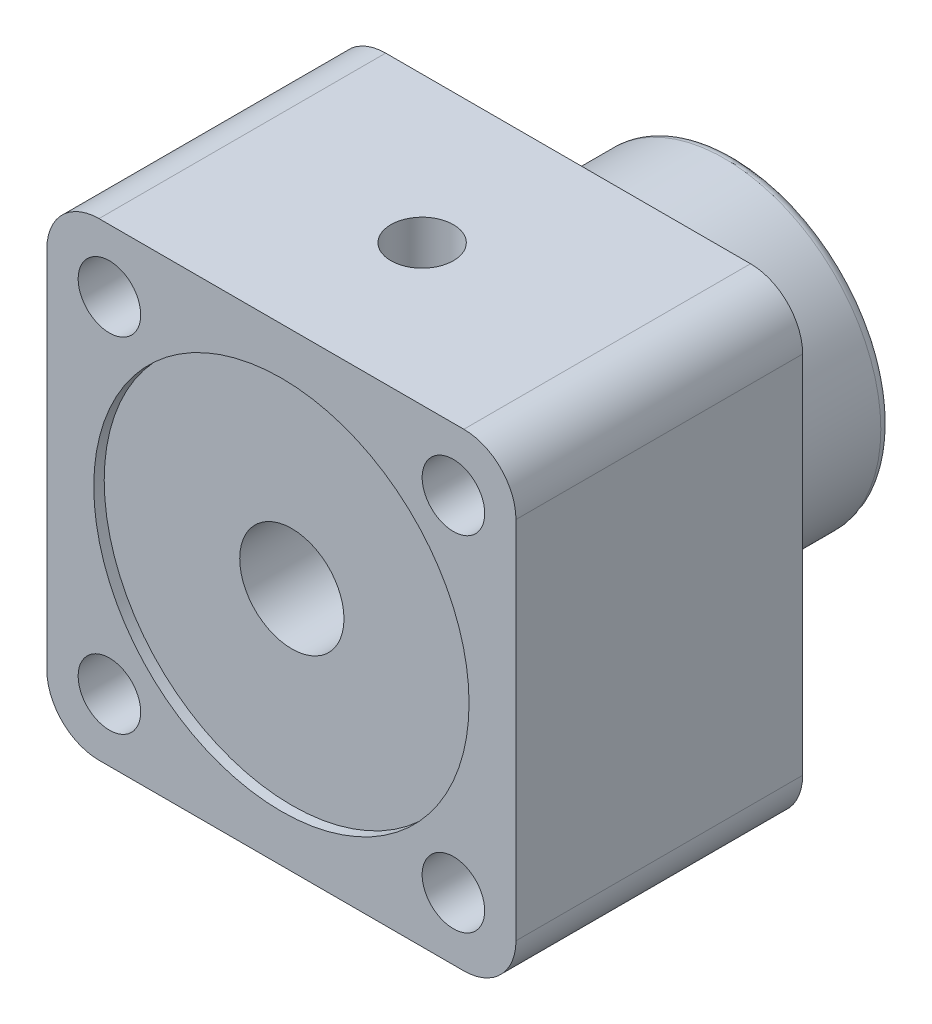
SolidWorks part; units mm, degrees
ref_plane "Front Plane" through (0, 0, 0) normal (0, 0, 1) x (1, 0, 0)
ref_plane "Top Plane" through (0, 0, 0) normal (0, 1, 0) x (1, 0, 0)
ref_plane "Right Plane" through (0, 0, 0) normal (1, 0, 0) x (0, 0, -1)
sketch "Sketch1" plane through (0, 0, 0) normal (0, 0, 1) x (1, 0, 0)
  line L0 (0, 40) -> (0, 5)
  line L1 (-5, 45) -> (-40, 45)
  line L2 (-45, 40) -> (-45, 5)
  line L3 (-40, 0) -> (-5, 0)
  line L6 (-45, 0) -> (0, 45) construction
  line L9 (-45, 45) -> (0, 0) construction
  circle A0 centre (-6, 39) radius 3
  circle A1 centre (-6, 6) radius 3
  circle A2 centre (-39, 6) radius 3
  circle A3 centre (-39, 39) radius 3
  arc A4 (-40, 45) -> (-45, 40) centre (-40, 40) ccw
  arc A5 (0, 40) -> (-5, 45) centre (-5, 40) ccw
  arc A6 (-45, 5) -> (-40, 0) centre (-40, 5) ccw
  arc A7 (-5, 0) -> (0, 5) centre (-5, 5) ccw
  dimension "D5" = 6
  dimension "D7" = 5
  dimension "D8" = 5
  dimension "D9" = 5
  dimension "D2" = 45
  dimension "D3" = 45
  dimension "D11" = 33
extrude "Boss-Extrude1" add sketch "Sketch1" along normal blind 27.5
sketch "Sketch3" plane through (0, 0, 27.5) normal (0, 0, 1) x (1, 0, 0)
  line L0 (-43.5355, 1.4645) -> (-1.4645, 43.5355) construction
  line L1 (-43.5355, 43.5355) -> (-1.4645, 1.4645) construction
  arc A0 (-45, 5) -> (-40, 0) centre (-40, 5) ccw construction
  arc A1 (0, 40) -> (-5, 45) centre (-5, 40) ccw construction
  arc A2 (-40, 45) -> (-45, 40) centre (-40, 40) ccw construction
  arc A3 (-5, 0) -> (0, 5) centre (-5, 5) ccw construction
  circle A4 centre (-22.5, 22.5) radius 18
  dimension "D1" = 36
extrude "Cut-Extrude1" cut sketch "Sketch3" against normal blind 1
sketch "Sketch4" plane through (0, 0, 0) normal (0, 0, -1) x (-1, 0, 0)
  line L0 (0, 5) -> (0, 40) construction
  line L1 (5, 45) -> (40, 45) construction
  circle A0 centre (22.5, 22.5) radius 5
  dimension "D1" = 10
  dimension "D2" = 22.5
  dimension "D3" = 22.5
extrude "Cut-Extrude2" cut sketch "Sketch4" against normal through all
sketch "Sketch5" plane through (0, 0, 0) normal (0, 0, -1) x (-1, 0, 0)
  circle A0 centre (22.5, 22.5) radius 15
  circle A1 centre (22.5, 22.5) radius 5 construction
  circle A2 centre (22.5, 22.5) radius 5
  dimension "D1" = 30
extrude "Boss-Extrude2" add sketch "Sketch5" along normal blind 16
fillet "Fillet1" radius 1 1 edges at (-37.5, 22.5, -16)
sketch "Sketch6" plane through (0, 45, 0) normal (0, 1, 0) x (1, 0, 0)
  line L0 (-45, -27.5) -> (-45, 0) construction
  line L2 (-5, 0) -> (-40, 0) construction
  circle A0 centre (-22.5, -14) radius 3
  dimension "D1" = 6
  dimension "D2" = 22.5
  dimension "D3" = 14
extrude "Cut-Extrude3" cut sketch "Sketch6" against normal up to surface (18.5 mm away)
